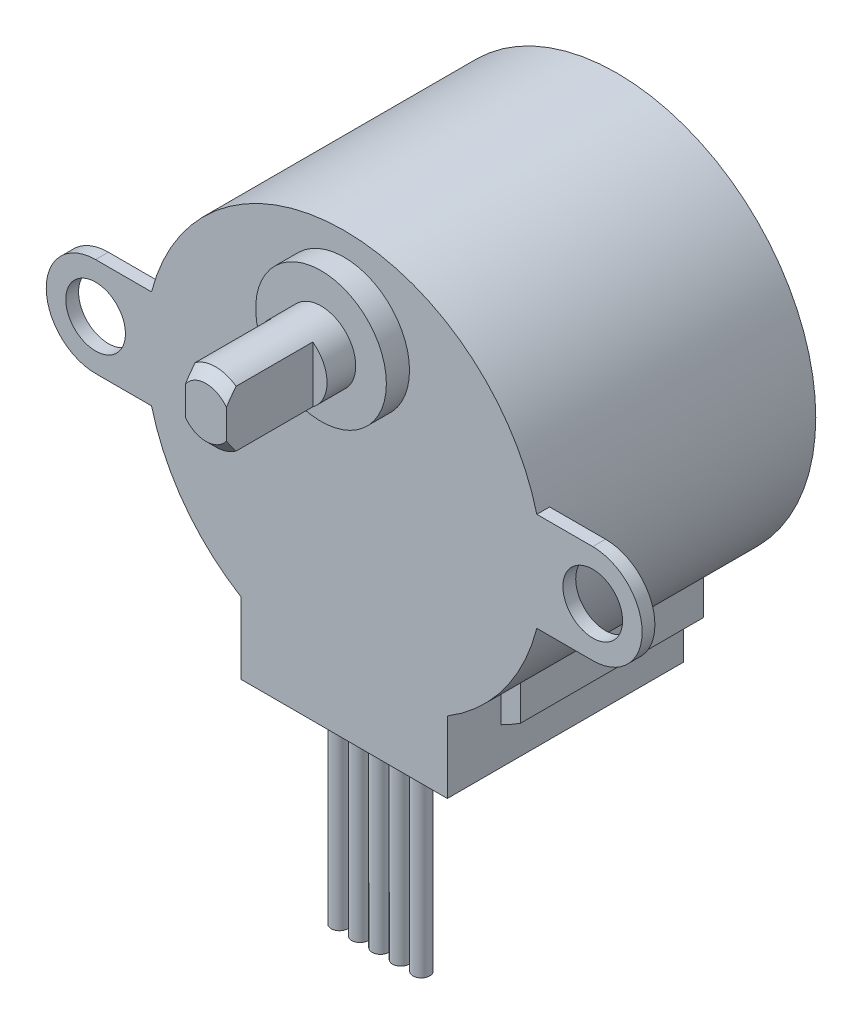
SolidWorks part; units mm, degrees
ref_plane "Front Plane" through (0, 0, 0) normal (0, 0, 1) x (1, 0, 0)
ref_plane "Top Plane" through (0, 0, 0) normal (0, 1, 0) x (1, 0, 0)
ref_plane "Right Plane" through (0, 0, 0) normal (1, 0, 0) x (0, 0, -1)
sketch "Sketch1" plane through (0, 0, 0) normal (0, 0, 1) x (1, 0, 0)
  line L0 (0, 0) -> (36.1502, 0) construction
  line L1 (10.56, 0) -> (-10.56, 0) construction
  line L2 (0, 0) -> (0, -23.3369) construction
  line L3 (0, -10.56) -> (0, 10.56) construction
  circle A0 centre (0, 0) radius 14
  dimension "D1" = 28
extrude "Boss-Extrude1" add sketch "Sketch1" against normal blind 19.2
sketch "Sketch2" plane through (0, 0, 0) normal (0, 0, 1) x (1, 0, 0)
  line L0 (-7.265, -11.9674) -> (-7.265, -17)
  line L1 (-7.265, -17) -> (7.265, -17)
  line L2 (7.265, -17) -> (7.265, -11.9674)
  line L3 (0, -14) -> (0, -520.9917) construction
  line L4 (0, -10.56) -> (0, 10.56) construction
  line L5 (10.56, 0) -> (-10.56, 0) construction
  circle A0 centre (0, 0) radius 14 construction
  arc A1 (-7.265, -11.9674) -> (7.265, -11.9674) centre (0, 0) ccw
  dimension "D1" = 17
  dimension "D2" = 14.53
extrude "Boss-Extrude2" add sketch "Sketch2" against normal offset from surface (16.64 mm away) 2.56 up to face at (14, 0, -19.2)
sketch "Sketch3" plane through (0, 0, -16.64) normal (0, 0, -1) x (-1, 0, 0)
  line L0 (7.265, -17) -> (7.265, -11.9674) construction
  line L1 (-7.265, -11.9674) -> (-7.265, -17) construction
  line L2 (7.265, -14.3901) -> (7.265, -11.9674)
  line L3 (-7.265, -11.9674) -> (-7.265, -14.3901)
  line L4 (8.645, -11.012) -> (8.645, -13.6058)
  line L5 (-8.645, -11.012) -> (-8.645, -13.6058)
  line L6 (0, 0) -> (0, -22.2748) construction
  line L7 (0, 10.56) -> (0, -10.56) construction
  circle A1 centre (0, 0) radius 14 construction
  circle A2 centre (0, 0) radius 16.12
  arc A3 (7.265, -14.3901) -> (8.645, -13.6058) centre (0, 0) ccw
  arc A4 (7.265, -11.9674) -> (8.645, -11.012) centre (0, 0) ccw
  arc A5 (-8.645, -13.6058) -> (-7.265, -14.3901) centre (0, 0) ccw
  arc A6 (-8.645, -11.012) -> (-7.265, -11.9674) centre (0, 0) ccw
  dimension "D2" = 17.29
  dimension "D1" = 2.12
extrude "Boss-Extrude3" add sketch "Sketch3" against normal offset from surface (12.87 mm away) 3.77 up to face at (0, -7.9919, 0)
sketch "Sketch4" plane through (0, -17, 0) normal (0, -1, 0) x (1, 0, 0)
  line L0 (0, -10.56) -> (0, 10.56) construction
  line L1 (-3.465, -1.97) -> (3.465, -1.97) construction
  line L2 (-3.465, -1.97) -> (-3.465, -3.14) construction
  line L3 (-3.465, -3.14) -> (3.465, -3.14) construction
  line L4 (3.465, -1.97) -> (3.465, -3.14) construction
  line L5 (-3.465, -1.97) -> (3.465, -3.14) construction
  line L6 (-3.465, -3.14) -> (3.465, -1.97) construction
  line L7 (0, -16.64) -> (0, -3.77) construction
  line L8 (31.4754, 0) -> (-31.4754, 0) construction
  line L9 (-3.465, -2.555) -> (3.465, -2.555) construction
  circle A0 centre (-2.88, -2.555) radius 0.585
  circle A1 centre (-1.44, -2.555) radius 0.585
  circle A2 centre (0, -2.555) radius 0.585
  circle A3 centre (1.44, -2.555) radius 0.585
  circle A4 centre (2.88, -2.555) radius 0.585
  point P0 (0, -2.555)
  dimension "D1" = 1.17
  dimension "D2" = 6.93
  dimension "D3" = 1.97
  dimension "D4" = 5
extrude "Boss-Extrude4" add sketch "Sketch4" along normal blind 14
sketch "Sketch5" plane through (0, 0, 0) normal (0, 0, 1) x (1, 0, 0)
  line L0 (0, -10.56) -> (0, 10.56) construction
  line L1 (10.56, 0) -> (-10.56, 0) construction
  circle A0 centre (0, 7.77) radius 4.6
  arc A1 (7.265, -11.9674) -> (-7.265, -11.9674) centre (0, 0) ccw construction
  point P4 (0, 14)
  point P7 (0, 12.37)
  dimension "D1" = 9.2
  dimension "D2" = 7.77
  dimension "D3" = 1.63
extrude "Boss-Extrude5" add sketch "Sketch5" along normal blind 1.63
sketch "Sketch6" plane through (0, 0, 1.63) normal (0, 0, 1) x (1, 0, 0)
  circle A0 centre (0, 7.77) radius 2.445
  dimension "D1" = 4.89
extrude "Boss-Extrude6" add sketch "Sketch6" along normal blind 8.1
sketch "Sketch7" plane through (0, 0, 9.73) normal (0, 0, 1) x (1, 0, 0)
  line L0 (0, 7.77) -> (0, 10.215) construction
  line L1 (1.44, 9.746) -> (1.44, 5.794)
  line L2 (-1.44, 9.746) -> (-1.44, 5.794)
  arc A0 (-1.44, 9.746) -> (-1.44, 5.794) centre (0, 7.77) ccw
  circle A1 centre (0, 7.77) radius 2.445
  arc A2 (1.44, 5.794) -> (1.44, 9.746) centre (0, 7.77) ccw
  circle A3 centre (0, 7.77) radius 2.445 construction
  circle A4 centre (0, 7.77) radius 2.445 construction
  dimension "D2" = 2.88
  dimension "D1" = 0
extrude "Cut-Extrude1" cut sketch "Sketch7" against normal blind 6.08
chamfer "Chamfer1" distance 0.68 angle 45 2 edges at (0, 10.215, 9.73) (0, 5.325, 9.73)
sketch "Sketch8" plane through (0, 0, 0) normal (0, 0, 1) x (1, 0, 0)
  line L0 (-14, 0) -> (-24.423, 0) construction
  line L1 (10.56, 0) -> (-10.56, 0) construction
  line L2 (-13.5619, 3.475) -> (-17.5, 3.475)
  line L3 (-17.5, -3.475) -> (-13.5619, -3.475)
  line L4 (0, 0) -> (0, -15.0566) construction
  line L5 (0, -10.56) -> (0, 10.56) construction
  line L6 (14, 0) -> (24.423, 0) construction
  line L7 (17.5, -3.475) -> (13.5619, -3.475)
  line L8 (13.5619, 3.475) -> (17.5, 3.475)
  arc A0 (7.265, -11.9674) -> (-7.265, -11.9674) centre (0, 0) ccw construction
  arc A1 (-13.5619, 3.475) -> (-13.5619, -3.475) centre (0, 0) ccw
  arc A2 (-17.5, 3.475) -> (-17.5, -3.475) centre (-17.5, 0) ccw
  circle A3 centre (-17.5, 0) radius 2.1
  circle A4 centre (17.5, 0) radius 2.1
  arc A5 (17.5, 3.475) -> (17.5, -3.475) centre (17.5, 0) cw
  arc A6 (13.5619, 3.475) -> (13.5619, -3.475) centre (0, 0) cw
  dimension "D2" = 4.2
  dimension "D1" = 6.95
  dimension "D3" = 35
extrude "Boss-Extrude7" add sketch "Sketch8" against normal blind 0.9
